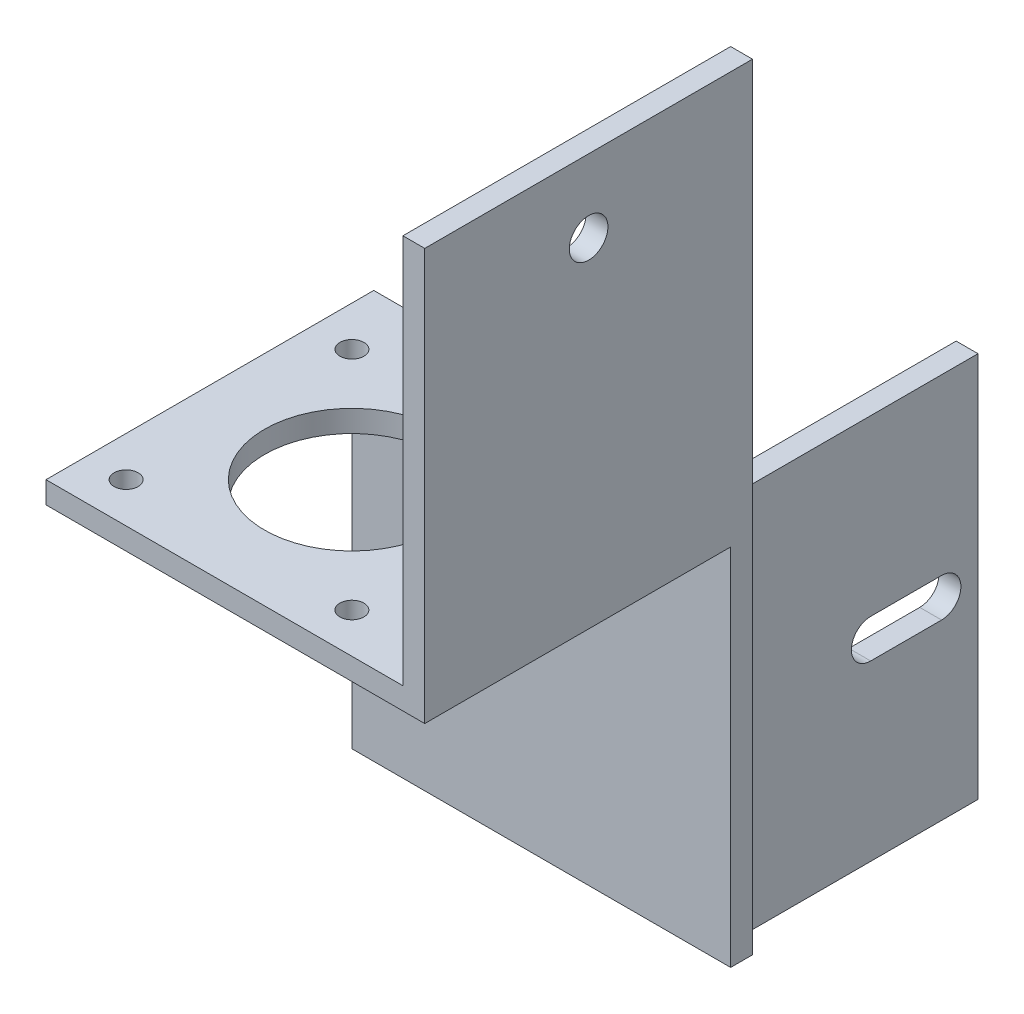
SolidWorks part; units mm, degrees
ref_plane "前视基准面" through (0, 0, 0) normal (0, 0, 1) x (1, 0, 0)
ref_plane "上视基准面" through (0, 0, 0) normal (0, 1, 0) x (1, 0, 0)
ref_plane "右视基准面" through (0, 0, 0) normal (1, 0, 0) x (0, 0, -1)
sketch "草图1" plane through (0, 0, 0) normal (0, 0, 1) x (1, 0, 0)
  line L1 (-18.194, 11.3599) -> (23.806, 11.3599)
  line L2 (-18.194, 11.3599) -> (-18.194, -41.6401)
  line L3 (-18.194, -41.6401) -> (23.806, -41.6401)
  line L4 (23.806, 11.3599) -> (23.806, -41.6401)
  dimension "D1" = 42
  dimension "D2" = 53
extrude "凸台-拉伸1" add sketch "草图1" along normal blind 3
sketch "草图2" plane through (0, 0, 3) normal (0, 0, 1) x (1, 0, 0)
  line L1 (23.806, -41.6401) -> (23.806, 11.3599) construction
  line L7 (-18.194, 11.3599) -> (23.806, 11.3599)
  line L8 (-18.194, 11.3599) -> (-18.194, 8.3599)
  line L9 (-18.194, 8.3599) -> (23.806, 8.3599)
  line L10 (23.806, 11.3599) -> (23.806, 8.3599)
  dimension "D2" = 3
extrude "凸台-拉伸2" add sketch "草图2" along normal blind 42
sketch "草图3" plane through (0, 8.3599, 0) normal (0, -1, 0) x (1, 0, 0)
  line L0 (-18.194, 45) -> (23.806, 45) construction
  line L1 (23.806, 45) -> (23.806, 3) construction
  circle A0 centre (2.806, 24) radius 12
  circle A1 centre (18.306, 39.5) radius 1.65
  circle A2 centre (18.306, 8.5) radius 1.65
  circle A3 centre (-12.694, 8.5) radius 1.65
  circle A4 centre (-12.694, 39.5) radius 1.65
  point P17 (2.806, 24)
  dimension "D1" = 24
  dimension "D2" = 3.3
  dimension "D3" = 5.5
  dimension "D4" = 5.5
  dimension "D5" = 4
extrude "切除-拉伸1" cut sketch "草图3" against normal through all
sketch "草图4" plane through (23.806, 0, 0) normal (1, 0, 0) x (0, 0, -1)
  line L1 (-45, 8.3599) -> (-3, 8.3599)
  line L2 (-45, 8.3599) -> (-45, 11.3599)
  line L3 (-45, 11.3599) -> (0, 11.3599)
  line L4 (0, 8.3599) -> (0, 11.3599)
  line L5 (0, -41.6401) -> (-3, -41.6401)
  line L6 (0, -41.6401) -> (0, 8.3599)
  line L8 (-3, -41.6401) -> (-3, 8.3599)
extrude "凸台-拉伸3" add sketch "草图4" along normal blind 10
sketch "草图5" plane through (0, 11.3599, 0) normal (0, 1, 0) x (1, 0, 0)
  line L0 (33.806, -45) -> (-18.194, -45) construction
  line L1 (33.806, 0) -> (30.806, 0)
  line L2 (33.806, 0) -> (33.806, -45)
  line L3 (33.806, -45) -> (30.806, -45)
  line L4 (30.806, 0) -> (30.806, -45)
  dimension "D1" = 3
extrude "凸台-拉伸4" add sketch "草图5" along normal blind 53.5
sketch "草图6" plane through (33.806, 0, 0) normal (1, 0, 0) x (0, 0, -1)
  line L0 (-45, 64.8599) -> (0, 64.8599) construction
  circle A0 centre (-22.5, 54.8599) radius 2.65
  dimension "D1" = 5.3
  dimension "D2" = 10
extrude "切除-拉伸2" cut sketch "草图6" against normal blind 20
sketch "草图7" plane through (0, 0, 0) normal (0, 0, -1) x (-1, 0, 0)
  line L5 (18.194, -41.6401) -> (-33.806, -41.6401) construction
  line L6 (-30.806, 11.3599) -> (18.194, 11.3599) construction
  line L7 (-30.806, -41.6401) -> (-27.806, -41.6401)
  line L8 (-30.806, -41.6401) -> (-30.806, 11.3599)
  line L9 (-30.806, 11.3599) -> (-27.806, 11.3599)
  line L10 (-27.806, -41.6401) -> (-27.806, 11.3599)
  line L11 (-33.806, -41.6401) -> (-33.806, 64.8599) construction
  dimension "D1" = 3
  dimension "D2" = 3
extrude "凸台-拉伸5" add sketch "草图7" along normal blind 33.96
sketch "草图10" plane through (30.806, 0, 0) normal (1, 0, 0) x (0, 0, -1)
  line L0 (28.96, -15.1577) -> (19.2249, -15.1577) construction
  line L1 (28.96, -17.8077) -> (19.2249, -17.8077)
  line L2 (28.96, -12.5077) -> (19.2249, -12.5077)
  line L3 (33.96, 11.3599) -> (33.96, -41.6401) construction
  arc A1 (28.96, -17.8077) -> (28.96, -12.5077) centre (28.96, -15.1577) ccw
  arc A2 (19.2249, -12.5077) -> (19.2249, -17.8077) centre (19.2249, -15.1577) ccw
  point P4 (24.0924, -15.1577)
  dimension "D1" = 5
  dimension "D2" = 2.65
extrude "切除-拉伸4" cut sketch "草图10" against normal blind 33.96
